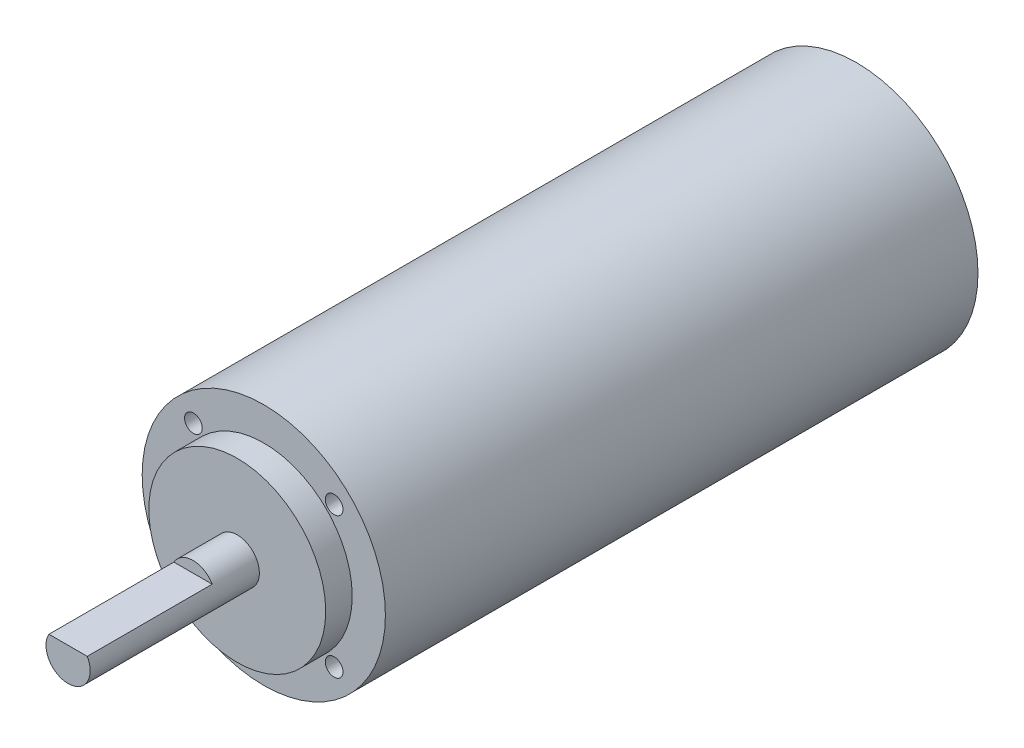
SolidWorks part; units mm, degrees
ref_plane "Front Plane" through (0, 0, 0) normal (0, 0, 1) x (1, 0, 0)
ref_plane "Top Plane" through (0, 0, 0) normal (0, 1, 0) x (1, 0, 0)
ref_plane "Right Plane" through (0, 0, 0) normal (1, 0, 0) x (0, 0, -1)
sketch "Sketch3" plane through (0, 0, 0) normal (0, 0, 1) x (1, 0, 0)
  line L0 (1.7321, 1) -> (-1.7321, 1)
  line L1 (0, 0) -> (0, 2) construction
  circle A0 centre (0, 0) radius 9
  circle A1 centre (0, 0) radius 11
  arc A2 (-1.7321, 1) -> (1.7321, 1) centre (0, 0) ccw
  arc A3 (0, 2) -> (-1.7321, 1) centre (0, 0) ccw construction
  arc A4 (1.7321, 1) -> (0, 2) centre (0, 0) ccw construction
  point P7 (0, 1)
  dimension "D1" = 18
  dimension "D2" = 22
  dimension "D3" = 4
sketch "Sketch4" plane through (0, 0, 0) normal (1, 0, 0) x (0, 0, -1)
  line L0 (0, 0) -> (4.4998, 0) construction
  line L7 (0, 8) -> (0, 11)
  line L8 (0, 11) -> (21.4, 11)
  line L9 (21.4, 11) -> (53.6, 11)
  line L10 (53.6, 11) -> (53.6, 0)
  line L11 (53.6, 0) -> (0, 0)
  line L12 (0, 8) -> (-2.4, 8)
  line L13 (-2.4, 8) -> (-2.4, 2)
  line L14 (-2.4, 2) -> (-17.7, 2)
  line L15 (-17.7, 2) -> (-17.7, 0)
  line L16 (-17.7, 0) -> (0, 0)
  line L17 (0, 0) -> (0, 8) construction
  point P2 (-18.9976, 1.2201)
  point P11 (0, 0)
  point P15 (-2.4, 7.7892)
  point P18 (-2.4, 6.0848)
  dimension "D1" = 15.3
  dimension "D2" = 71.3
  dimension "D3" = 21.4
  dimension "D4" = 32.2
  dimension "D5" = 16
revolve "Revolve1" add sketch "Sketch4" angle 360 about L0
sketch "Sketch5" plane through (0, 0, 17.7) normal (0, 0, 1) x (1, 0, 0)
  line L0 (1.7321, 1) -> (-1.7321, 1) construction
  line L1 (1.7321, 1) -> (-1.7321, 1)
  arc A2 (1.7321, 1) -> (0, 2) centre (0, 0) ccw construction
  arc A3 (0, 2) -> (-1.7321, 1) centre (0, 0) ccw construction
  arc A4 (1.7321, 1) -> (0, 2) centre (0, 0) ccw
  arc A5 (0, 2) -> (-1.7321, 1) centre (0, 0) ccw
extrude "Cut-Extrude1" cut sketch "Sketch5" against normal offset from surface (11.3 mm away) 4 up to face at (2, 0, 2.4)
hole_wizard "Tap Drill for M2x0.4 Tap1" positions "Sketch7" profile "Sketch8" hole size "M2x0.4" standard "ANSI Metric"
sketch "Sketch7" plane through (0, 0, 0) normal (0, 0, 1) x (1, 0, 0)
  circle A0 centre (0, 0) radius 9 construction
  point P0 (6.364, 6.364)
  point P9 (6.364, -6.364)
  point P10 (-6.364, -6.364)
  point P11 (-6.364, 6.364)
  point P13 (-6.5795, 6.1409)
  point P14 (6.7464, 5.957)
  point P15 (-6.7426, 5.9613)
  point P16 (-6.3638, -6.3641)
  dimension "D1" = 4
sketch "Sketch8" plane through (6.364, 6.364, 0) normal (1, 0, 0) x (0, -1, 0)
  line L0 (0, 0) -> (0, 4.4807)
  line L1 (0, 4.4807) -> (0.8, 4)
  line L2 (0.8, 4) -> (0.8, 0)
  line L5 (0.8, 0) -> (0, 0)
  line L10 (0, 4.4807) -> (-0.8, 4) construction
  line L11 (0, -6.35) -> (0, 107.95) construction
  dimension "Hole Dia." = 1.6
  dimension "Hole Depth" = 4
  dimension "Drill Angle" = 118
